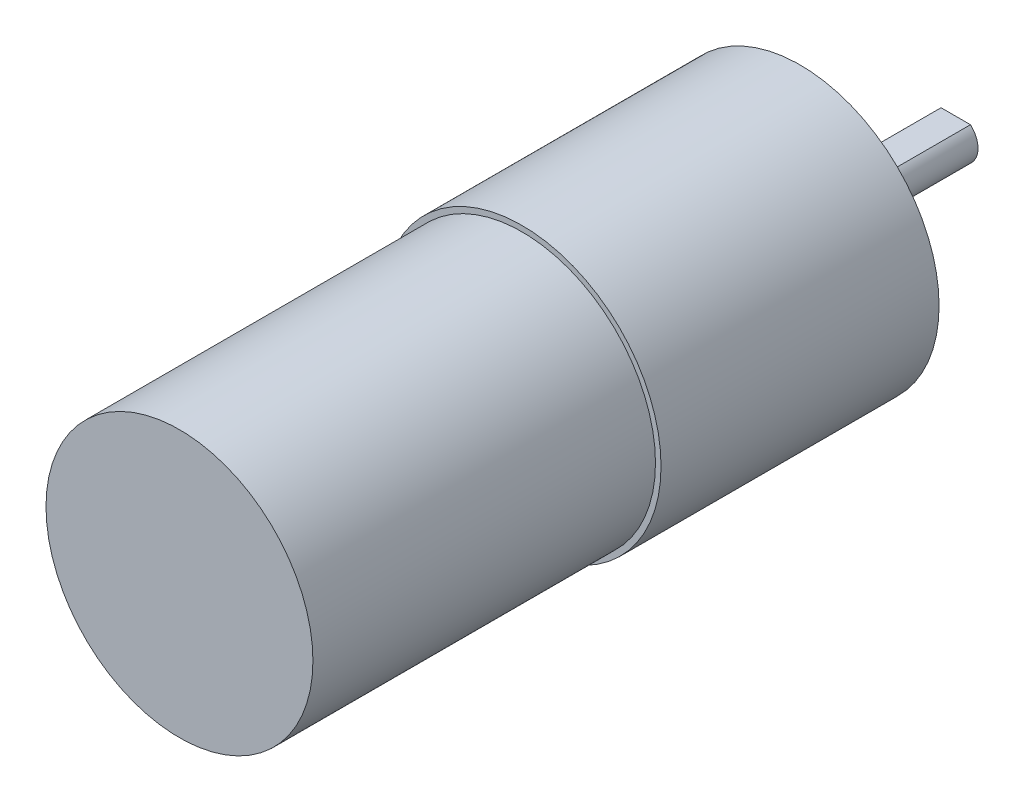
SolidWorks part; units mm, degrees
ref_plane "Front Plane" through (0, 0, 0) normal (0, 0, 1) x (1, 0, 0)
ref_plane "Top Plane" through (0, 0, 0) normal (0, 1, 0) x (1, 0, 0)
ref_plane "Right Plane" through (0, 0, 0) normal (1, 0, 0) x (0, 0, -1)
sketch "Sketch1" plane through (0, 0, 0) normal (0, 0, 1) x (1, 0, 0)
  circle A0 centre (0, 0) radius 12.5
extrude "Boss-Extrude2" add sketch "Sketch1" along normal blind 25
sketch "Sketch2" plane through (0, 0, 0) normal (0, 0, -1) x (-1, 0, 0)
  circle A0 centre (0, 0) radius 3
extrude "Boss-Extrude3" add sketch "Sketch2" along normal blind 2
sketch "Sketch3" plane through (0, 0, -2) normal (0, 0, -1) x (-1, 0, 0)
  circle A0 centre (0, 0) radius 2
extrude "Boss-Extrude4" add sketch "Sketch3" along normal blind 12
sketch "Sketch4" plane through (0, 0, -14) normal (0, 0, -1) x (-1, 0, 0)
  line L0 (-1.3229, 1.5) -> (1.3229, 1.5)
  circle A0 centre (0, 0) radius 2 construction
  circle A1 centre (0, 0) radius 2 construction
  arc A2 (-1.3229, 1.5) -> (1.3229, 1.5) centre (0, 0) cw
  dimension "D1" = 1.5
extrude "Cut-Extrude1" cut sketch "Sketch4" against normal blind 12
sketch "Sketch5" plane through (0, 0, 25) normal (0, 0, 1) x (1, 0, 0)
  circle A0 centre (0, 0) radius 12
extrude "Boss-Extrude5" add sketch "Sketch5" along normal blind 30.8
